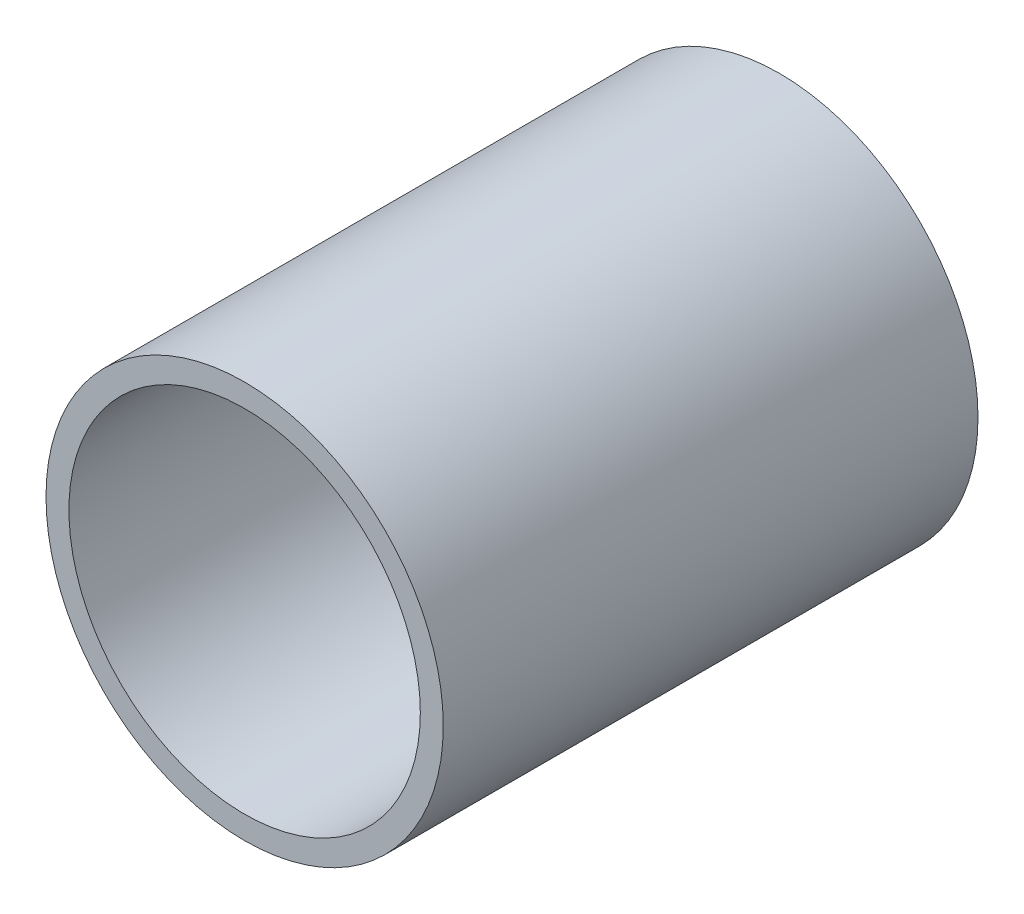
SolidWorks part; units mm, degrees
ref_plane "Front Plane" through (0, 0, 0) normal (0, 0, 1) x (1, 0, 0)
ref_plane "Top Plane" through (0, 0, 0) normal (0, 1, 0) x (1, 0, 0)
ref_plane "Right Plane" through (0, 0, 0) normal (1, 0, 0) x (0, 0, -1)
sketch "Sketch2" plane through (0, 0, 0) normal (0, 1, 0) x (1, 0, 0)
  line L0 (0, 0) -> (0, 70) construction
  line L1 (23, 0) -> (23, 70)
  line L2 (23, 70) -> (26, 70)
  line L3 (26, 70) -> (26, 0)
  line L4 (26, 0) -> (23, 0)
  point P5 (0, 27.78)
  point P8 (0, 53.7601)
  point P9 (0, 70)
  dimension "D1" = 23
  dimension "D2" = 26
  dimension "D3" = 70
revolve "Revolve1" add sketch "Sketch2" angle 360 about L0
